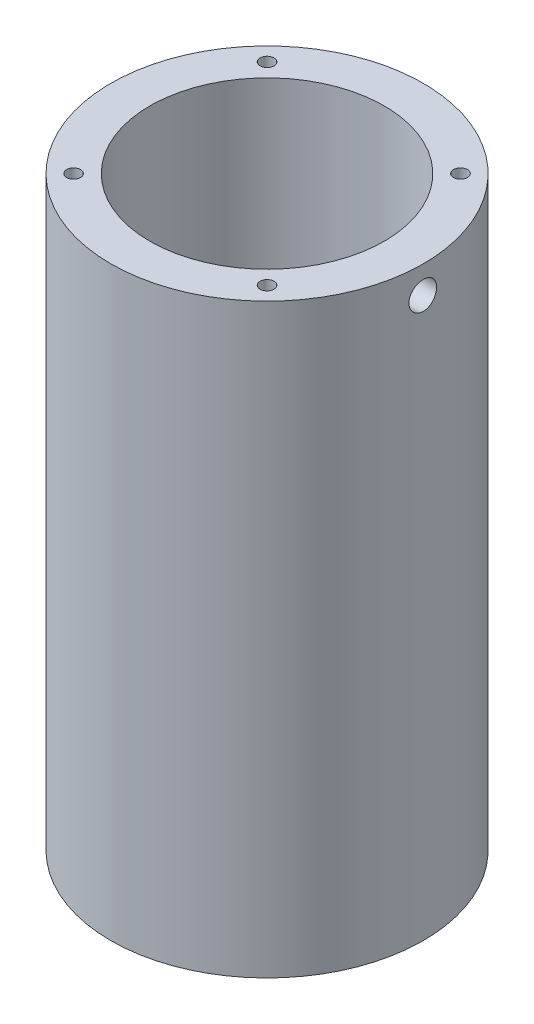
SolidWorks part; units mm, degrees
material "Delrin 2700 NC010, Low Viscosity Acetal Copolymer (SS)"
ref_plane "Front Plane" through (0, 0, 0) normal (0, 0, 1) x (1, 0, 0)
ref_plane "Top Plane" through (0, 0, 0) normal (0, 1, 0) x (1, 0, 0)
ref_plane "Right Plane" through (0, 0, 0) normal (1, 0, 0) x (0, 0, -1)
sketch "Sketch1" plane through (0, 0, 0) normal (0, 1, 0) x (1, 0, 0)
  circle A0 centre (0, 0) radius 19.05
  circle A1 centre (0, 0) radius 25.4
  dimension "D1" = 38.1
  dimension "D2" = 6.35
extrude "Boss-Extrude1" add sketch "Sketch1" along normal blind 95.25 contours A0 | A1
hole_wizard "#4-40 Tapped Hole1" positions "Sketch3" profile "Sketch2" tap size "#4-40" standard "ANSI Inch"
sketch "Sketch3" plane through (0, 0, 0) normal (0, -1, 0) x (-1, 0, 0)
  line L8 (0, 0) -> (15.7154, 15.7154) construction
  line L10 (0, 0) -> (0, 13.4294) construction
  point P3 (15.7154, 15.7154)
  point P39 (15.7154, -15.7154)
  point P40 (-15.7154, -15.7154)
  point P41 (-15.7154, 15.7154)
  point P42 (0, 0)
  dimension "D1" = 4
  dimension "D2" = 22.225
  dimension "D3" = 45
sketch "Sketch2" plane through (-15.7154, 0, -15.7154) normal (1, 0, 0) x (0, 0, -1)
  line L0 (0, 0) -> (0, 8.9342)
  line L1 (0, 8.9342) -> (1.1303, 8.255)
  line L2 (1.1303, 8.255) -> (1.1303, 0)
  line L5 (1.1303, 0) -> (0, 0)
  line L10 (0, 8.9342) -> (-1.1303, 8.255) construction
  line L11 (0, -6.35) -> (0, 107.95) construction
  dimension "Tap Drill Dia." = 2.2606
  dimension "Tap Drill Depth" = 8.255
  dimension "Drill Angle" = 118
ref_plane "Plane1" through (0, 47.625, 0) normal (0, -1, 0) x (-1, 0, 0)
mirror "Mirror1" about plane through (0, 47.625, 0) normal (0, -1, 0) of "#4-40 Tapped Hole1"
hole_wizard "#8 Clearance Hole1" positions "Sketch8" profile "Sketch7" hole size "#8" standard "ANSI Inch"
sketch "Sketch8" plane through (0, 0, 0) normal (1, 0, 0) x (0, 0, -1)
  line L0 (25.4, 95.25) -> (-25.4, 95.25) construction
  point P0 (0, 90.805)
  dimension "D1" = 4.445
sketch "Sketch7" plane through (0, 90.805, 0) normal (0, 1, 0) x (0, 0, 1)
  line L0 (0, 0) -> (0, 25.4)
  line L1 (0, 25.4) -> (2.2479, 25.4)
  line L2 (2.2479, 25.4) -> (2.2479, 0)
  line L5 (2.2479, 0) -> (0, 0)
  line L11 (0, -6.35) -> (0, 107.95) construction
  dimension "Thru Hole Dia." = 4.4958
  dimension "Thru Hole Depth" = 25.4
